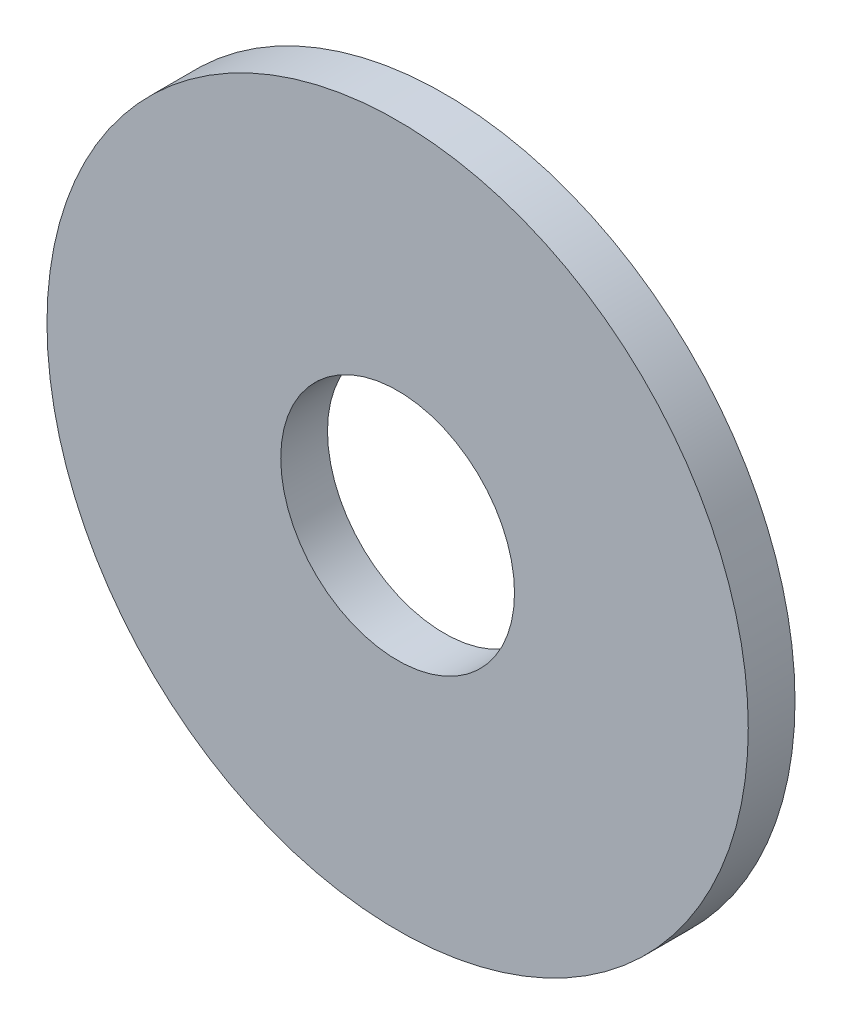
SolidWorks part; units mm, degrees
ref_plane "Ön Düzlem" through (0, 0, 0) normal (0, 0, 1) x (1, 0, 0)
ref_plane "Üst Düzlem" through (0, 0, 0) normal (0, 1, 0) x (1, 0, 0)
ref_plane "Sağ Düzlem" through (0, 0, 0) normal (1, 0, 0) x (0, 0, -1)
sketch "Sketch1" plane through (0, 0, 0) normal (0, 0, 1) x (1, 0, 0)
  circle A0 centre (0, 0) radius 2.5
  circle A1 centre (0, 0) radius 7.5
  dimension "D1" = 5
  dimension "D2" = 15
extrude "Boss-Extrude1" add sketch "Sketch1" along normal blind 1
